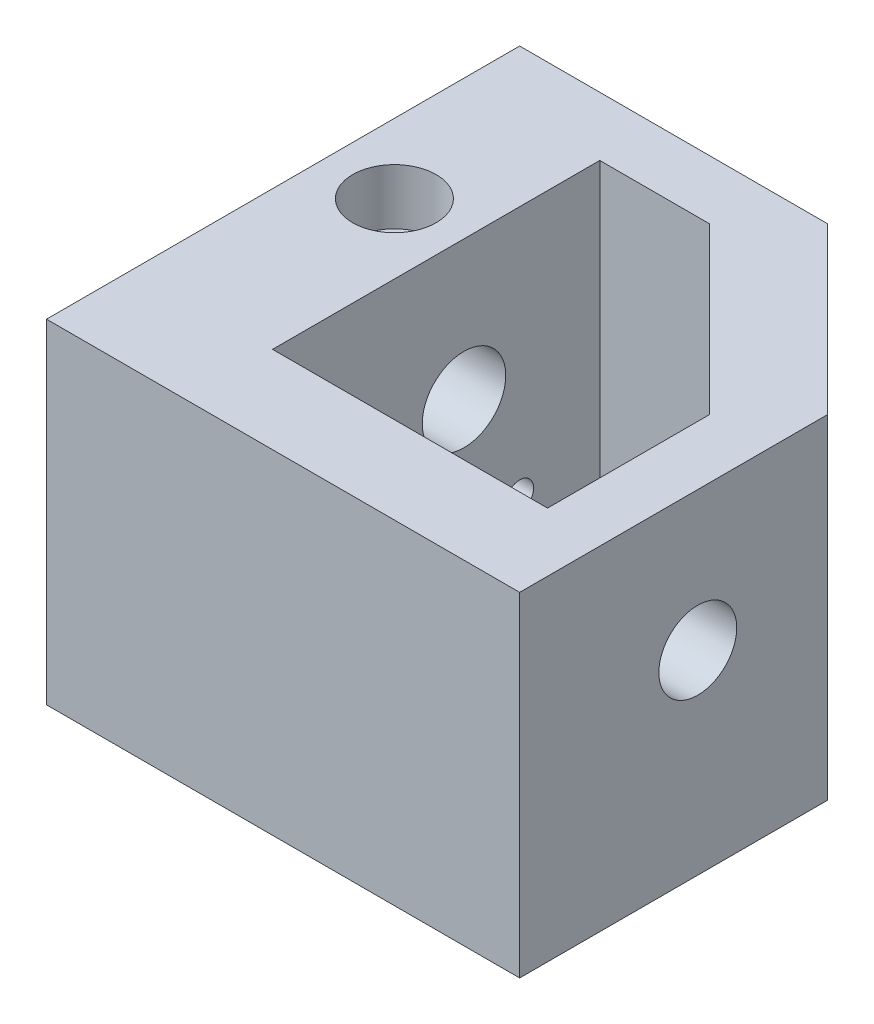
SolidWorks part; units mm, degrees
ref_plane "Front Plane" through (0, 0, 0) normal (0, 0, 1) x (1, 0, 0)
ref_plane "Top Plane" through (0, 0, 0) normal (0, 1, 0) x (1, 0, 0)
ref_plane "Right Plane" through (0, 0, 0) normal (1, 0, 0) x (0, 0, -1)
sketch "Sketch1" plane through (0, 0, 0) normal (0, 1, 0) x (1, 0, 0)
  line L0 (-42.7058, 39.6026) -> (-42.7058, -40.3974)
  line L1 (-42.7058, -40.3974) -> (42.2942, -40.3974)
  line L2 (42.2942, -40.3974) -> (42.2942, 9.9041)
  line L3 (12.5957, 39.6026) -> (42.2942, 9.9041)
  line L4 (-42.7058, 39.6026) -> (12.5957, 39.6026)
  line L5 (-17.7058, 28.9926) -> (-17.7058, -29.7874)
  line L6 (-17.7058, -29.7874) -> (31.691, -29.7874)
  line L7 (31.691, -29.7874) -> (31.691, -0.7059)
  line L8 (-17.7058, 28.9926) -> (1.9925, 28.9926)
  line L9 (1.9925, 28.9926) -> (31.691, -0.7059)
  dimension "D1" = 80
  dimension "D2" = 85
  dimension "D3" = 42
  dimension "D4" = 135
  dimension "D5" = 25
  dimension "D6" = 10.61
  dimension "D7" = 15
  dimension "D8" = 42
  dimension "D9" = 10.61
extrude "Boss-Extrude2" add sketch "Sketch1" along normal blind 60
sketch "Sketch4" plane through (0, 0, 0) normal (0, -1, 0) x (-1, 0, 0)
  line L0 (17.7058, 28.9926) -> (-1.9925, 28.9926)
  line L1 (-1.9925, 28.9926) -> (-31.691, -0.7059)
  line L2 (-31.691, -0.7059) -> (-31.691, -29.7874)
  line L3 (-31.691, -29.7874) -> (17.7058, -29.7874)
  line L4 (17.7058, -29.7874) -> (17.7058, 28.9926)
extrude "Boss-Extrude3" add sketch "Sketch4" against normal blind 10
sketch "Sketch8" plane through (26.0992, 0, -26.0992) normal (0.7071, 0, -0.7071) x (-0.7071, 0, -0.7071)
  line L0 (-22.9032, 60) -> (-22.9032, 0) construction
  line L1 (-20.9032, 54) -> (17.0968, 54) construction
  line L2 (-20.9032, 54) -> (-20.9032, 16) construction
  line L3 (-20.9032, 16) -> (17.0968, 16) construction
  line L4 (17.0968, 54) -> (17.0968, 16) construction
  line L5 (-22.9032, 60) -> (19.0968, 60) construction
  circle A0 centre (11.0968, 48) radius 4.75
  circle A1 centre (11.0968, 34) radius 3
  circle A2 centre (11.0968, 22) radius 4.75
  circle A3 centre (-0.9032, 22) radius 3
  circle A4 centre (-14.9032, 22) radius 4.75
  dimension "D3" = 9.5
  dimension "D5" = 9.5
  dimension "D6" = 6
  dimension "D7" = 9.5
  dimension "D10" = 6
  dimension "D11" = 6
  dimension "D12" = 6
  dimension "D15" = 6
  dimension "D16" = 6
  dimension "D18" = 18
  dimension "D1" = 38
  dimension "D2" = 38
  dimension "D4" = 6
  dimension "D8" = 6
  dimension "D9" = 6
  dimension "D13" = 6
  dimension "D14" = 18
  dimension "D17" = 6
  dimension "D19" = 6
  dimension "D20" = 2
extrude "Cut-Extrude2" cut sketch "Sketch8" against normal up to next
sketch "Sketch9" plane through (-42.7058, 0, 0) normal (-1, 0, 0) x (0, 0, 1)
  line L0 (-39.6026, 60) -> (-39.6026, 0) construction
  line L2 (-39.6026, 60) -> (40.3974, 60) construction
  circle A0 centre (-4.6026, 35) radius 7.5
  dimension "D3" = 15
  dimension "D1" = 35
  dimension "D2" = 25
extrude "Cut-Extrude3" cut sketch "Sketch9" against normal up to next
sketch "Sketch10" plane through (42.2942, 0, 0) normal (1, 0, 0) x (0, 0, -1)
  line L0 (-40.3974, 60) -> (9.9041, 60) construction
  line L1 (-40.3974, 60) -> (-40.3974, 0) construction
  circle A0 centre (-13.3974, 35) radius 7
  dimension "D2" = 27
  dimension "D3" = 14
  dimension "D1" = 25
extrude "Cut-Extrude4" cut sketch "Sketch10" against normal up to next
sketch "Sketch12" plane through (0, 60, 0) normal (0, 1, 0) x (1, 0, 0)
  line L0 (12.5957, 39.6026) -> (-42.7058, 39.6026) construction
  line L2 (-42.7058, 39.6026) -> (-42.7058, -40.3974) construction
  circle A0 centre (-30.2058, 4.6026) radius 7.5
  dimension "D2" = 12.5
  dimension "D3" = 15
  dimension "D1" = 35
extrude "Cut-Extrude6" cut sketch "Sketch12" against normal blind 10
sketch "Sketch24" plane through (0, 50, 0) normal (0, 1, 0) x (1, 0, 0)
  line L0 (-30.2058, 4.6026) -> (-22.7058, 4.6026) construction
  line L1 (-30.2058, 4.6026) -> (-37.7058, 4.6026) construction
  circle A0 centre (-30.2058, 4.6026) radius 7.5 construction
  circle A1 centre (-26.4558, 4.6026) radius 2.25
  circle A2 centre (-33.9558, 4.6026) radius 2.25
  dimension "D1" = 4.5
  dimension "D2" = 4.5
extrude "Cut-Extrude16" cut sketch "Sketch24" against normal up to next
sketch "Sketch33" plane through (-42.7058, 0, 0) normal (-1, 0, 0) x (0, 0, 1)
  circle A0 centre (5.3974, 38) radius 1.5
  circle A1 centre (-4.6026, 35) radius 7.5 construction
  circle A2 centre (5.3974, 32) radius 1.5
  dimension "D1" = 3
  dimension "D2" = 10
  dimension "D3" = 3
  dimension "D5" = 10
  dimension "D6" = 3
  dimension "D4" = 6
extrude "Cut-Extrude18" cut sketch "Sketch33" against normal blind 10
sketch "Sketch37" plane through (0, 0, 40.3974) normal (0, 0, 1) x (1, 0, 0)
  line L1 (42.2942, 60) -> (-42.7058, 60)
  line L2 (42.2942, 60) -> (42.2942, 0)
  line L3 (42.2942, 0) -> (-42.7058, 0)
  line L4 (-42.7058, 60) -> (-42.7058, 0)
extrude "Boss-Extrude7" add sketch "Sketch37" along normal blind 5
sketch "Sketch38" plane through (-42.7058, 0, 0) normal (-1, 0, 0) x (0, 0, 1)
  line L0 (-39.6026, 0) -> (45.3974, 0) construction
  line L1 (-39.6026, 60) -> (-39.6026, 0) construction
  line L2 (45.3974, 60) -> (45.3974, 0) construction
  line L3 (-39.6026, 60) -> (45.3974, 60) construction
  circle A0 centre (-19.6026, 5) radius 2.5
  circle A1 centre (25.3974, 5) radius 2.5
  circle A2 centre (-36.8526, 40) radius 2
  circle A3 centre (42.6474, 40) radius 2
  dimension "D1" = 4
  dimension "D2" = 5
  dimension "D3" = 5
  dimension "D4" = 4
  dimension "D5" = 5
  dimension "D6" = 5
  dimension "D7" = 2.75
  dimension "D8" = 2.75
  dimension "D9" = 20
  dimension "D10" = 20
  dimension "D11" = 20
  dimension "D12" = 20
extrude "Cut-Extrude19" cut sketch "Sketch38" against normal blind 20
sketch "Sketch39" plane through (-42.7058, 0, 0) normal (-1, 0, 0) x (0, 0, 1)
  line L0 (-39.6026, 0) -> (45.3974, 0) construction
  line L1 (-39.6026, 60) -> (-39.6026, 0) construction
  circle A0 centre (-14.6026, 15) radius 2.5
  dimension "D1" = 5
  dimension "D2" = 15
  dimension "D3" = 25
extrude "Cut-Extrude20" cut sketch "Sketch39" against normal up to next
sketch "Sketch40" plane through (0, 0, 0) normal (0, -1, 0) x (1, 0, 0)
  line L0 (12.5957, -39.6026) -> (-42.7058, -39.6026) construction
  line L1 (-42.7058, -39.6026) -> (-42.7058, 45.3974) construction
  line L2 (-42.7058, 45.3974) -> (42.2942, 45.3974) construction
  line L3 (42.2942, 45.3974) -> (42.2942, -9.9041) construction
  line L4 (42.2942, -9.9041) -> (12.5957, -39.6026) construction
  circle A0 centre (-36.7058, -33.6026) radius 2
  circle A1 centre (-36.7058, 39.3974) radius 2
  circle A2 centre (36.2942, 39.3974) radius 2
  circle A3 centre (36.2942, -7.4189) radius 2
  circle A4 centre (10.1104, -33.6026) radius 2
  dimension "D1" = 4
  dimension "D2" = 4
  dimension "D3" = 4
  dimension "D4" = 4
  dimension "D5" = 4
  dimension "D6" = 6
  dimension "D7" = 6
  dimension "D8" = 6
  dimension "D9" = 6
  dimension "D10" = 6
  dimension "D11" = 6
  dimension "D12" = 6
  dimension "D13" = 6
  dimension "D14" = 6
  dimension "D15" = 6
extrude "Cut-Extrude21" cut sketch "Sketch40" against normal blind 10
sketch "Sketch41" plane through (26.0992, 0, -26.0992) normal (0.7071, 0, -0.7071) x (-0.7071, 0, -0.7071)
  circle A0 centre (14.0968, 34) radius 1.15
  circle A1 centre (11.0968, 34) radius 3 construction
  circle A2 centre (8.0968, 34) radius 1.15
  circle A3 centre (-0.9032, 25) radius 1.15
  circle A4 centre (-0.9032, 22) radius 3 construction
  circle A5 centre (-0.9032, 19) radius 1.15
  dimension "D1" = 2.3
  dimension "D2" = 2.3
  dimension "D3" = 2.3
  dimension "D4" = 2.3
extrude "Cut-Extrude22" cut sketch "Sketch41" against normal blind 2.5
